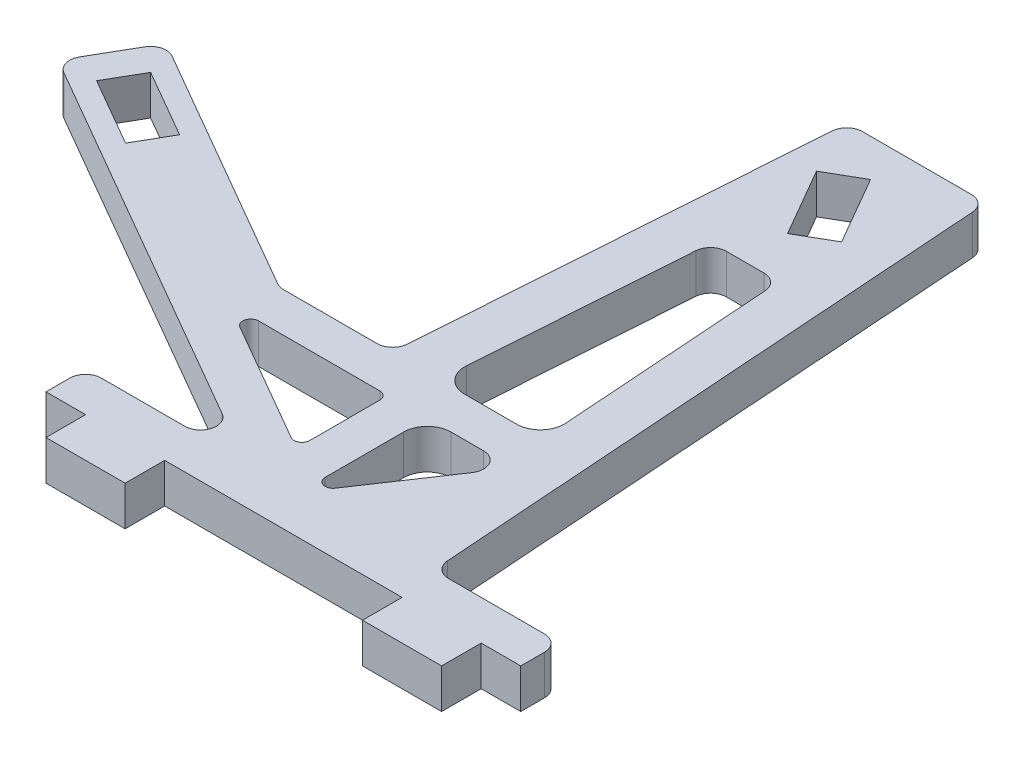
SolidWorks part; units mm, degrees
ref_plane "前视基准面" through (0, 0, 0) normal (0, 0, 1) x (1, 0, 0)
ref_plane "上视基准面" through (0, 0, 0) normal (0, 1, 0) x (1, 0, 0)
ref_plane "右视基准面" through (0, 0, 0) normal (1, 0, 0) x (0, 0, -1)
other "Configuration Table"
sketch "草图1" plane through (0, 0, 0) normal (0, 1, 0) x (1, 0, 0)
  line L0 (-5, 5) -> (0, 5)
  line L1 (0, 5) -> (0, 0)
  line L2 (0, 0) -> (10, 0)
  line L3 (10, 0) -> (10, 5)
  line L4 (10, 5) -> (40, 5)
  line L5 (40, 5) -> (40, 0)
  line L6 (40, 0) -> (50, 0)
  line L7 (50, 0) -> (50, 5)
  line L8 (50, 5) -> (55, 5)
  line L9 (55, 5) -> (55, 10)
  line L11 (-5, 10) -> (-5, 5)
  line L12 (55, 10) -> (39, 10)
  line L13 (39, 10) -> (33.75, 85.0785)
  line L15 (-40.5268, 42.0584) -> (15, 10)
  line L16 (15, 10) -> (-5, 10)
  line L17 (-40.5268, 42.0584) -> (-35.5268, 50.7187)
  line L18 (-35.5268, 50.7187) -> (-1.7152, 31.1975)
  line L19 (-1.7152, 31.1975) -> (12.4823, 31.1975)
  line L22 (-26.9683, -5) -> (80.0491, -5) construction
  line L38 (-29.0642, 56.8032) -> (-29.0642, -18.1084) construction
  line L39 (-30.5781, 44.8824) -> (36.0487, 6.4154) construction
  line L40 (-62.8643, 24.4938) -> (67.0395, 99.4938) construction
  line L41 (33.75, 85.0785) -> (16.25, 85.0785)
  line L42 (16.25, 85.0785) -> (12.4823, 31.1975)
  line L43 (-24.694, 41.5776) -> (-33.3543, 46.5776) construction
  line L44 (25, 5) -> (25, 71.8118) construction
  line L45 (-29.0242, 44.0776) -> (-29.0642, 44.0083) construction
  point P31 (-29.0242, 44.0776)
  point P32 (25, 85.0785)
  point P35 (13.3808, 68.5139)
  point P76 (25, 5)
  dimension "D1" = 10
  dimension "D2" = 10
  dimension "D3" = 30
  dimension "D4" = 5
  dimension "D5" = 5
  dimension "D6" = 5
  dimension "D7" = 5
  dimension "D8" = 49.0083
  dimension "D9" = 49.0112
  dimension "D10" = 10
  dimension "D11" = 30
  dimension "D12" = 94
  dimension "D13" = 94
  dimension "D14" = 5
  dimension "D15" = 16
  dimension "D16" = 17.5
  dimension "D17" = 30
  dimension "D18" = 39.0423
  dimension "D19" = 20
  dimension "D20" = 14.1975
extrude "凸台-拉伸1" add sketch "草图1" along normal blind 5 contours L13 L12 L9 L8 L7 L6 L5 L4 L3 L2 L1 L0 L11 L16 L15 L17 L18 L19 L42 L41
sketch "草图2" plane through (0, 5, 0) normal (0, 1, 0) x (1, 0, 0)
  line L0 (-35.8543, 42.2475) -> (-27.194, 37.2475)
  line L1 (-27.194, 37.2475) -> (-24.694, 41.5776)
  line L2 (-24.694, 41.5776) -> (-33.3543, 46.5776)
  line L3 (-33.3543, 46.5776) -> (-35.8543, 42.2475)
  line L7 (-47.9585, 33.0997) -> (41.1945, 84.5722) construction
  line L8 (28.8684, 71.6822) -> (23.8684, 80.3425)
  line L9 (23.8684, 80.3425) -> (19.5383, 77.8425)
  line L10 (19.5383, 77.8425) -> (24.5383, 69.1822)
  line L11 (24.5383, 69.1822) -> (28.8684, 71.6822)
  line L12 (-42.618, 51.8336) -> (-14.3494, 35.5128) construction
  line L13 (-29.0242, 44.0776) -> (-29.0642, 44.0083) construction
  line L14 (-24.694, 41.5776) -> (-33.3543, 46.5776) construction
  line L15 (-40.5268, 42.0584) -> (15, 10) construction
  line L16 (-199975, -5) -> (200040.9362, -5) construction
  line L17 (-29.0242, 44.0776) -> (-29.0642, 44.0083) construction
  line L18 (-3.055, 26.1975) -> (17, 26.1975)
  line L19 (17, 26.1975) -> (17, 14.6188)
  line L20 (33.75, 85.0785) -> (16.25, 85.0785)
  line L21 (17, 14.6188) -> (-3.055, 26.1975)
  line L22 (39, 10) -> (33.75, 85.0785)
  line L23 (55, 10) -> (39, 10)
  line L24 (55, 5) -> (55, 10)
  line L25 (50, 5) -> (55, 5)
  line L26 (50, 0) -> (50, 5)
  line L27 (40, 0) -> (50, 0)
  line L28 (40, 5) -> (40, 0)
  line L29 (10, 5) -> (40, 5)
  line L30 (10, 0) -> (10, 5)
  line L31 (0, 0) -> (10, 0)
  line L32 (0, 5) -> (0, 0)
  line L33 (-5, 5) -> (0, 5)
  line L34 (-5, 10) -> (-5, 5)
  line L35 (15, 10) -> (-5, 10)
  line L36 (-40.5268, 42.0584) -> (15, 10)
  line L37 (-35.5268, 50.7187) -> (-40.5268, 42.0584)
  line L38 (-1.7152, 31.1975) -> (-35.5268, 50.7187)
  line L39 (12.4823, 31.1975) -> (-1.7152, 31.1975)
  line L42 (39, 10) -> (33.75, 85.0785)
  line L43 (55, 10) -> (39, 10)
  line L44 (55, 5) -> (55, 10)
  line L45 (50, 5) -> (55, 5)
  line L46 (50, 0) -> (50, 5)
  line L47 (40, 0) -> (50, 0)
  line L48 (40, 5) -> (40, 0)
  line L49 (10, 5) -> (40, 5)
  line L50 (10, 0) -> (10, 5)
  line L51 (0, 0) -> (10, 0)
  line L52 (0, 5) -> (0, 0)
  line L53 (-5, 5) -> (0, 5)
  line L54 (-5, 10) -> (-5, 5)
  line L55 (15, 10) -> (-5, 10)
  line L56 (-40.5268, 42.0584) -> (15, 10)
  line L57 (-35.5268, 50.7187) -> (-40.5268, 42.0584)
  line L58 (-1.7152, 31.1975) -> (-35.5268, 50.7187)
  line L59 (12.4823, 31.1975) -> (-1.7152, 31.1975)
  line L60 (20.75, 63.374) -> (29.25, 63.374)
  line L61 (29.25, 63.374) -> (31.5, 31.1975)
  line L62 (31.5, 31.1975) -> (18.5, 31.1975)
  line L63 (18.5, 31.1975) -> (20.75, 63.374)
  line L64 (22, 26.1975) -> (22, 10)
  line L65 (22, 10) -> (32.8551, 26.1975)
  line L66 (32.8551, 26.1975) -> (22, 26.1975)
  line L67 (25, 85.0785) -> (25, 91.9302) construction
  line L68 (33.75, 85.0785) -> (16.25, 85.0785)
  line L69 (16.25, 85.0785) -> (12.4823, 31.1975)
  line L70 (16.25, 85.0785) -> (12.4823, 31.1975)
  point P1 (22.0383, 73.5123)
  point P30 (-29.0242, 44.0776)
  point P46 (22.0383, 73.5123)
  point P48 (13.378, 68.5123)
  point P58 (25, 31.1975)
  point P59 (0, 0)
  point P60 (0, 0)
  point P61 (0, 0)
  point P62 (0, 0)
  point P63 (0, 0)
  dimension "D2" = 10
  dimension "D3" = 5
  dimension "D4" = 2.5
  dimension "D5" = 0.08
  dimension "D6" = 10
  dimension "D7" = 5
  dimension "D8" = 49.0083
  dimension "D9" = 49.008
  dimension "D10" = 5
  dimension "D11" = 5
  dimension "D12" = 10
  dimension "D13" = 5
  dimension "D14" = 5
  dimension "D15" = 5
  dimension "D16" = 7
  dimension "D17" = 0
  dimension "D18" = 13
  dimension "D19" = 8.5
  dimension "D1" = 0
extrude "切除-拉伸1" cut sketch "草图2" against normal through all contours L10 L7 L8 L9 | L7 L10 L11 L8 | L21 L19 L18 | L65 L66 L64 | L63 L62 L61 L60 | L3 L0 L1 L2
sketch3d "3D草图1"
  point P0 (-14.6833, 0.6455, -35.7979)
ref_plane "基准面2" through (11.7901, 0, -20.4211) normal (-0.5, 0, 0.866) x (0.866, 0, 0.5)
fillet "圆角1" radius 2 1 edges at (20.75, 2.5, -63.374)
fillet "圆角2" radius 2 1 edges at (29.25, 2.5, -63.374)
fillet "圆角3" radius 3 1 edges at (18.5, 2.5, -31.1975)
fillet "圆角4" radius 3 1 edges at (31.5, 2.5, -31.1975)
fillet "圆角5" radius 3 1 edges at (22, 2.5, -26.1975)
fillet "圆角6" radius 2 1 edges at (32.8551, 2.5, -26.1975)
fillet "圆角7" radius 1 1 edges at (22, 2.5, -10)
fillet "圆角8" radius 1 1 edges at (17, 2.5, -14.6188)
fillet "圆角9" radius 1 1 edges at (-3.055, 2.5, -26.1975)
fillet "圆角10" radius 1 1 edges at (17, 2.5, -26.1975)
fillet "圆角11" radius 2 1 edges at (-5, 2.5, -10)
fillet "圆角12" radius 2 1 edges at (55, 2.5, -10)
fillet "圆角13" radius 2 1 edges at (39, 2.5, -10)
fillet "圆角14" radius 2 1 edges at (15, 2.5, -10)
fillet "圆角15" radius 2 2 edges at (-35.5268, 2.5, -50.7187) (-40.5268, 2.5, -42.0584)
fillet "圆角16" radius 2 4 edges at (33.75, 2.5, -85.0785) (16.25, 2.5, -85.0785) (12.4823, 2.5, -31.1975) (-1.7152, 2.5, -31.1975)
